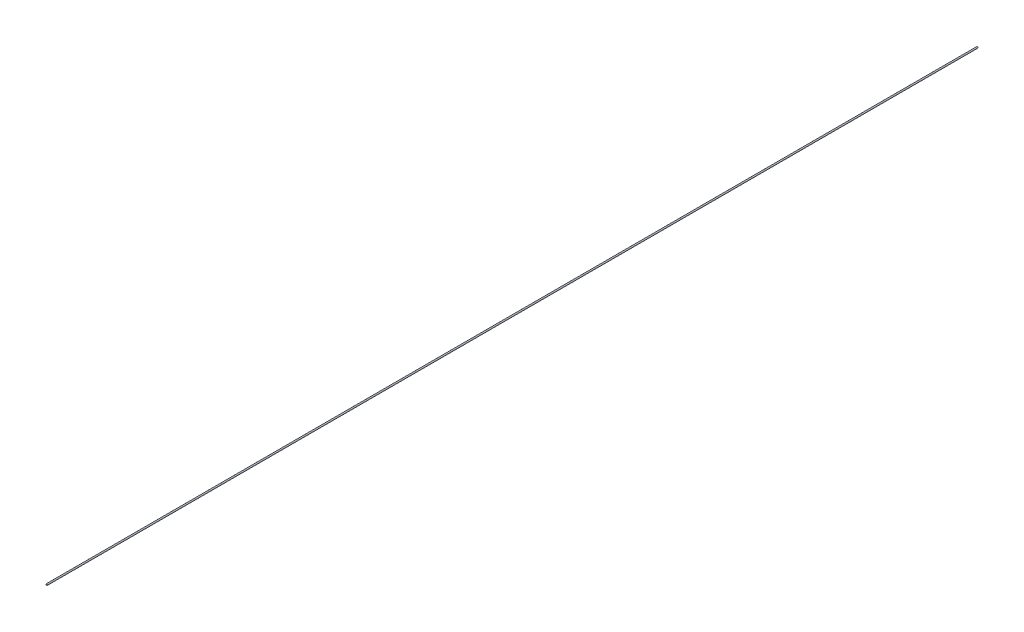
SolidWorks part; units mm, degrees
ref_plane "Front Plane" through (0, 0, 0) normal (0, 0, 1) x (1, 0, 0)
ref_plane "Top Plane" through (0, 0, 0) normal (0, 1, 0) x (1, 0, 0)
ref_plane "Right Plane" through (0, 0, 0) normal (1, 0, 0) x (0, 0, -1)
sketch "Sketch2" plane through (0, 0, 0) normal (0, 0, 1) x (1, 0, 0)
  line L2 (-306.005, -229.1739) -> (-303.005, -231.1739) construction
  circle A0 centre (-304.505, -230.1739) radius 1
  point P2 (-304.505, -230.1739)
  dimension "D1" = 2
extrude "Boss-Extrude1" add sketch "Sketch2" along normal blind 1357
